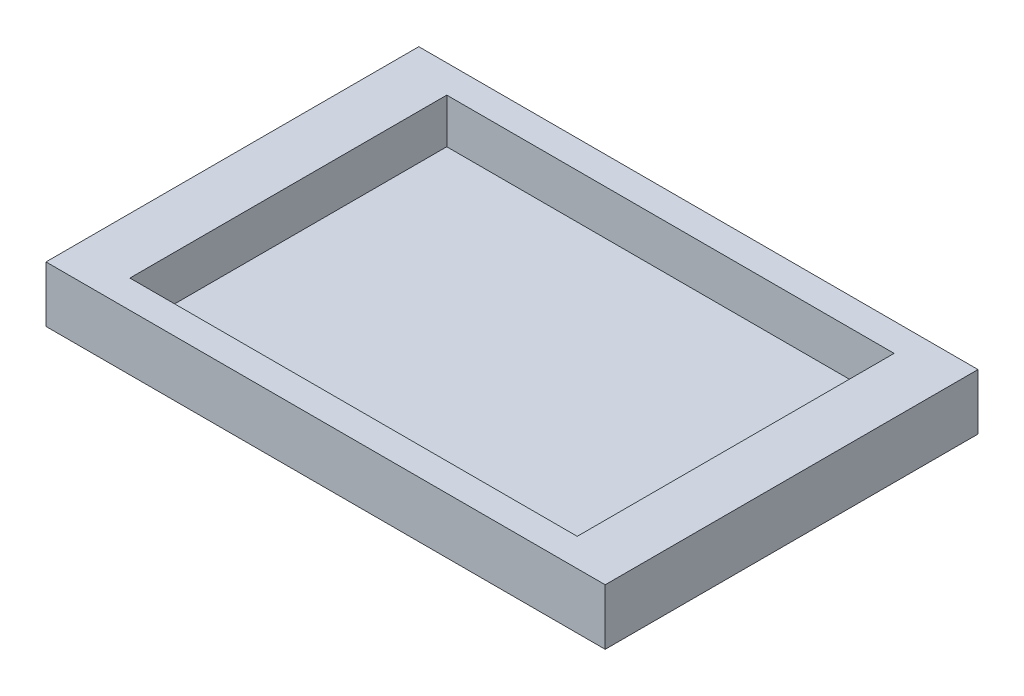
SolidWorks part; units mm, degrees
ref_plane "Спереди" through (0, 0, 0) normal (0, 0, 1) x (1, 0, 0)
ref_plane "Сверху" through (0, 0, 0) normal (0, 1, 0) x (1, 0, 0)
ref_plane "Справа" through (0, 0, 0) normal (1, 0, 0) x (0, 0, -1)
sketch "Эскиз1" plane through (0, 0, 0) normal (0, 1, 0) x (1, 0, 0)
  line L1 (-75, 50) -> (75, 50)
  line L2 (-75, 50) -> (-75, -50)
  line L3 (-75, -50) -> (75, -50)
  line L4 (75, 50) -> (75, -50)
  line L5 (-75, 50) -> (75, -50) construction
  line L6 (-75, -50) -> (75, 50) construction
  point P0 (0, 0)
extrude "Бобышка-Вытянуть1" add sketch "Эскиз1" along normal blind 15
sketch "Эскиз2" plane through (0, 15, 0) normal (0, 1, 0) x (1, 0, 0)
  line L1 (60, -42.5) -> (-60, -42.5)
  line L2 (60, -42.5) -> (60, 42.5)
  line L3 (60, 42.5) -> (-60, 42.5)
  line L4 (-60, -42.5) -> (-60, 42.5)
  line L5 (60, -42.5) -> (-60, 42.5) construction
  line L6 (60, 42.5) -> (-60, -42.5) construction
  point P0 (0, 0)
extrude "Вырез-Вытянуть1" cut sketch "Эскиз2" against normal blind 12
